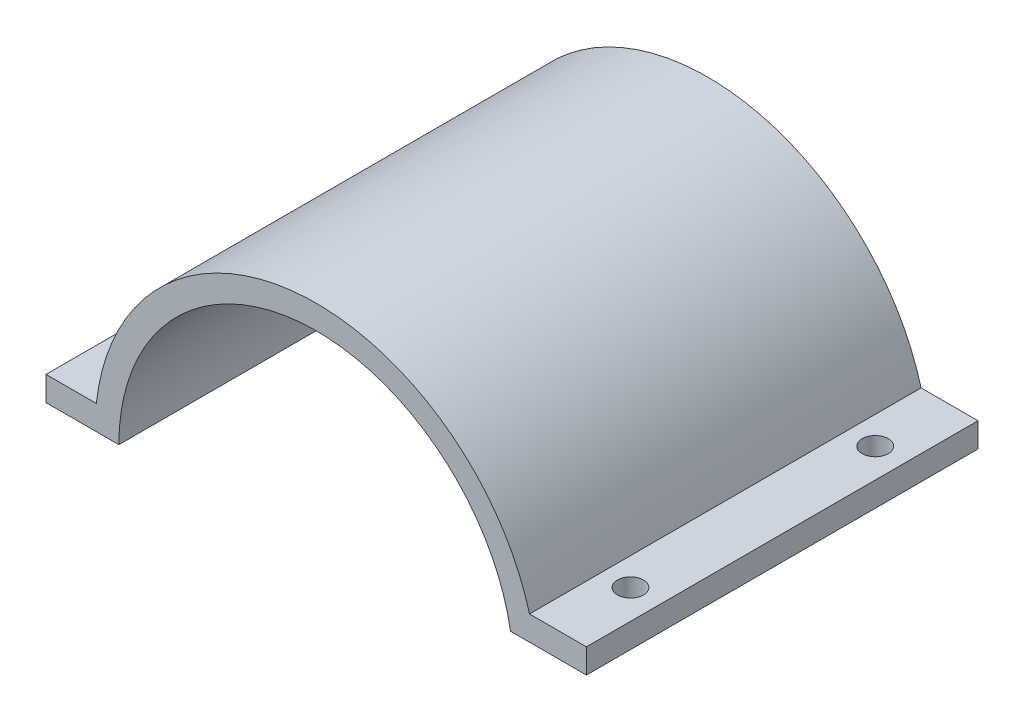
SolidWorks part; units mm, degrees
ref_plane "Front Plane" through (0, 0, 0) normal (0, 0, 1) x (1, 0, 0)
ref_plane "Top Plane" through (0, 0, 0) normal (0, 1, 0) x (1, 0, 0)
ref_plane "Right Plane" through (0, 0, 0) normal (1, 0, 0) x (0, 0, -1)
sketch "Sketch1" plane through (0, 0, 0) normal (0, 0, 1) x (1, 0, 0)
  line L0 (0, 0) -> (-57.404, 0) construction
  line L1 (0, 0) -> (57.404, 0) construction
  line L4 (-56.7112, -8.8915) -> (-56.7112, -57.404)
  line L5 (-56.7112, -57.404) -> (57.404, -57.404)
  line L6 (57.404, -57.404) -> (57.404, 0)
  line L7 (57.2303, 4.4627) -> (70.104, 4.4627)
  line L8 (70.104, 4.4627) -> (70.104, -57.404)
  line L9 (70.104, -57.404) -> (57.404, -57.404)
  line L10 (-56.7112, -8.8915) -> (-70.104, -8.8915)
  line L11 (-70.104, -8.8915) -> (-70.104, -57.404)
  line L12 (-70.104, -57.404) -> (-56.7112, -57.404)
  line L13 (-56.7112, -8.8915) -> (-56.7112, -57.404)
  line L14 (0, 0) -> (-13.2526, 49.4593)
  line L15 (-13.2526, 49.4593) -> (-13.2526, 55.8533)
  line L16 (0, 0) -> (-57.404, 0)
  line L17 (0, 0) -> (-57.404, 0)
  line L18 (-57.404, 0) -> (-70.104, 0)
  line L19 (-70.104, 0) -> (-70.104, 6.35)
  line L20 (0, 0) -> (-50.4261, -8.8915)
  line L21 (-50.4261, -8.8915) -> (-56.7112, -8.8915)
  line L22 (0, 0) -> (51.0092, 4.4627)
  line L23 (51.0092, 4.4627) -> (57.2303, 4.4627)
  line L24 (-70.104, 6.35) -> (-57.0517, 6.35)
  line L25 (0, 0) -> (13.2526, 49.4593)
  line L26 (13.2526, 49.4593) -> (13.2526, 55.8533)
  line L27 (0, 0) -> (50.4261, 8.8915)
  line L28 (70.104, 15.2415) -> (55.3436, 15.2415)
  line L29 (50.4261, 8.8915) -> (56.7112, 8.8915)
  line L30 (56.7112, 8.8915) -> (70.104, 8.8915)
  line L31 (70.104, 8.8915) -> (70.104, 15.2415)
  line L32 (0, 0) -> (0, 57.404) construction
  circle A0 centre (0, 0) radius 51.204
  circle A1 centre (0, 0) radius 57.404
  dimension "D1" = 102.408
  dimension "D3" = 5
  dimension "D4" = 175
  dimension "D5" = 12.7
  dimension "D6" = 12.7
  dimension "D8" = 6.35
  dimension "D10" = 5
  dimension "D11" = 6.35
  dimension "D7" = 15
  dimension "D9" = 15
  dimension "D2" = 6.2
extrude "Boss-Extrude1" add sketch "Sketch1" along normal mid plane 101.6
sketch "Sketch2" plane through (0, 6.35, 0) normal (0, 1, 0) x (1, 0, 0)
  line L0 (-62.484, 50.8) -> (-62.484, -50.8) construction
  line L1 (-70.104, 50.8) -> (-57.0517, 50.8) construction
  line L2 (-70.104, -50.8) -> (-57.0517, -50.8) construction
  line L3 (-70.104, -50.8) -> (-70.104, 50.8) construction
  point P6 (-62.484, 0)
  point P7 (-62.484, 31.75)
  point P8 (-62.484, -31.75)
  dimension "D1" = 7.62
  dimension "D2" = 31.75
  dimension "D3" = 31.75
hole_wizard "1/4 Clearance Hole1" positions "Sketch2" profile "Sketch3" hole size "1/4" standard "ANSI Inch"
sketch "Sketch3" plane through (-62.484, 6.35, 31.75) normal (1, 0, 0) x (0, 0, 1)
  line L0 (0, 0) -> (0, 6.35)
  line L1 (0, 6.35) -> (3.3782, 6.35)
  line L2 (3.3782, 6.35) -> (3.3782, 0)
  line L5 (3.3782, 0) -> (0, 0)
  line L11 (0, -6.35) -> (0, 107.95) construction
  dimension "Thru Hole Dia." = 6.7564
  dimension "Thru Hole Depth" = 6.35
sketch "Sketch4" plane through (0, 15.2415, 0) normal (0, 1, 0) x (1, 0, 0)
  line L0 (62.484, 50.8) -> (62.484, -50.8) construction
  line L1 (70.104, 50.8) -> (55.3436, 50.8) construction
  line L2 (70.104, -50.8) -> (55.3436, -50.8) construction
  line L3 (70.104, -50.8) -> (70.104, 50.8) construction
  point P6 (62.484, 0)
  point P7 (62.484, 31.75)
  point P8 (62.484, -31.75)
  dimension "D1" = 7.62
  dimension "D2" = 31.75
  dimension "D3" = 31.75
hole_wizard "1/4 Clearance Hole2" positions "Sketch4" profile "Sketch5" hole size "1/4" standard "ANSI Inch"
sketch "Sketch5" plane through (62.484, 15.2415, 31.75) normal (1, 0, 0) x (0, 0, 1)
  line L0 (0, 0) -> (0, 15.2415)
  line L1 (0, 15.2415) -> (3.3782, 15.2415)
  line L2 (3.3782, 15.2415) -> (3.3782, 0)
  line L5 (3.3782, 0) -> (0, 0)
  line L11 (0, -6.35) -> (0, 107.95) construction
  dimension "Thru Hole Dia." = 6.7564
  dimension "Thru Hole Depth" = 15.2415
equation "\"tolerance\" = 0.3mm"
equation "\"D1@Sketch1\"=4.02 + \"tolerance\""
equation "\"D2@Sketch1\"=0.25 - \"tolerance\"/2"
